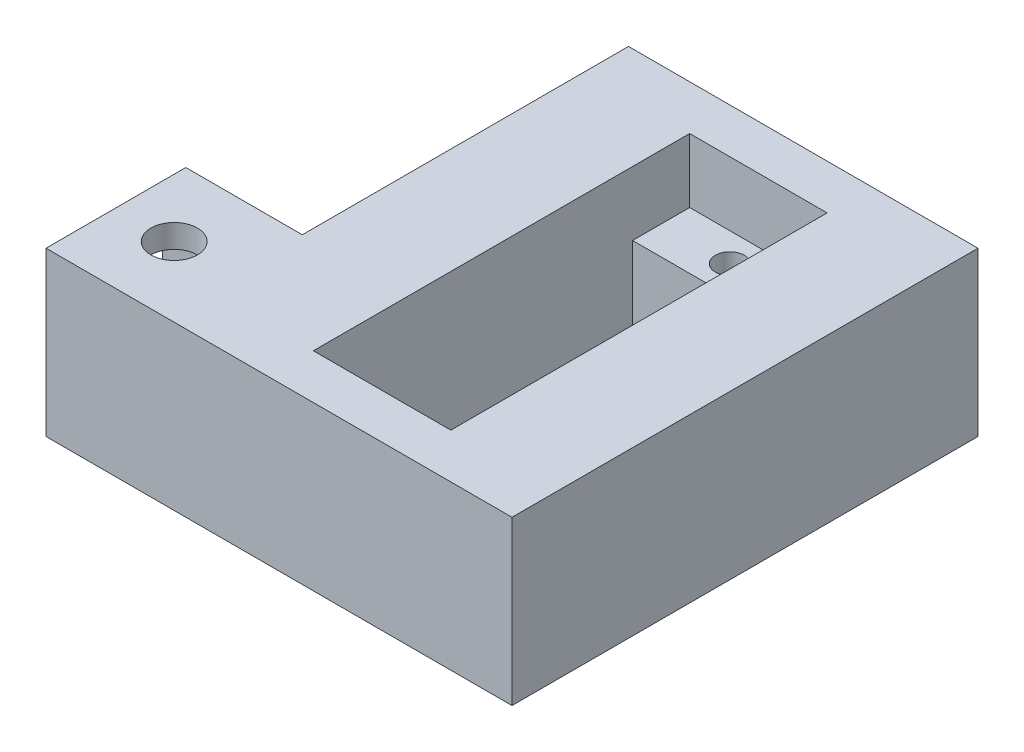
SolidWorks part; units mm, degrees
ref_plane "Front Plane" through (0, 0, 0) normal (0, 0, 1) x (1, 0, 0)
ref_plane "Top Plane" through (0, 0, 0) normal (0, 1, 0) x (1, 0, 0)
ref_plane "Right Plane" through (0, 0, 0) normal (1, 0, 0) x (0, 0, -1)
sketch "Sketch1" plane through (0, 0, 0) normal (0, 0, 1) x (1, 0, 0)
  line L1 (8.671, 9.0036) -> (-11.329, 9.0036)
  line L3 (11.4585, -4.9953) -> (8.671, -4.9953)
  line L5 (-11.329, -4.9953) -> (8.671, -4.9953)
  line L9 (8.671, 9.0036) -> (8.671, -4.9953)
  line L15 (-11.329, 9.0036) -> (-21.329, 9.0036)
  line L17 (-21.329, 9.0036) -> (-21.329, -4.9953)
  line L18 (-21.329, -4.9953) -> (-11.329, -4.9953)
  line L25 (18.8739, 13.2298) -> (8.671, 9.0036)
  line L26 (20.7873, 8.6104) -> (18.8739, 13.2298)
  line L27 (24.2314, 0.2955) -> (11.4585, -4.9953)
  line L28 (20.7873, 8.6104) -> (24.2314, 0.2955)
  dimension "D1" = 20
extrude "Boss-Extrude1" add sketch "Sketch1" along normal blind 40 contours L1 L15 L17 L18 L5 L9
sketch "Sketch3" plane through (0, 9.0036, 0) normal (0, 1, 0) x (1, 0, 0)
  line L0 (-6.329, -40) -> (-6.329, 0) construction
  line L1 (8.671, -40) -> (-21.329, -40) construction
  line L2 (-11.329, 0) -> (8.671, 0) construction
  line L3 (-21.329, -20) -> (8.671, -20) construction
  line L4 (-21.329, -40) -> (-21.329, 0) construction
  line L5 (8.671, -40) -> (8.671, 0) construction
  line L6 (-12.229, -31.25) -> (-0.429, -31.25)
  line L8 (-12.229, -3.85) -> (-12.229, -36.15)
  line L9 (-12.229, -36.15) -> (-0.429, -36.15)
  line L10 (-0.429, -3.85) -> (-0.429, -36.15)
  line L11 (-6.329, -31.25) -> (-6.329, -36.15) construction
  line L12 (-12.229, -3.85) -> (-0.429, -3.85)
  line L13 (-12.229, -8.75) -> (-0.429, -8.75)
  circle A0 centre (-6.329, -33.7) radius 1.25
  circle A1 centre (-6.329, -6.3) radius 1.25
  point P24 (-0.429, -20)
  point P26 (-12.229, -20)
  dimension "D1" = 11.8
  dimension "D2" = 5.9
  dimension "D3" = 16.15
  dimension "D4" = 4.9
sketch "Sketch4" plane through (0, 9.0036, 0) normal (0, 1, 0) x (1, 0, 0)
  line L0 (-12.229, -36.15) -> (-0.429, -36.15) construction
  line L1 (-0.429, -3.85) -> (-0.429, -36.15) construction
  line L2 (-12.229, -3.85) -> (-0.429, -3.85) construction
  line L3 (-12.229, -3.85) -> (-12.229, -36.15) construction
  line L4 (-12.229, -36.15) -> (-0.429, -36.15)
  line L5 (-0.429, -3.85) -> (-0.429, -36.15)
  line L6 (-12.229, -3.85) -> (-0.429, -3.85)
  line L7 (-12.229, -3.85) -> (-12.229, -36.15)
extrude "Cut-Extrude1" cut sketch "Sketch4" against normal blind 5.5
sketch "Sketch5" plane through (0, 3.5036, 0) normal (0, 1, 0) x (1, 0, 0)
  line L0 (-12.229, -31.25) -> (-0.429, -31.25) construction
  line L1 (-0.429, -3.85) -> (-0.429, -36.15) construction
  line L2 (-12.229, -3.85) -> (-12.229, -36.15) construction
  line L3 (-12.229, -8.75) -> (-0.429, -8.75) construction
  line L4 (-12.229, -31.25) -> (-0.429, -31.25)
  line L5 (-0.429, -8.75) -> (-0.429, -31.25)
  line L6 (-12.229, -8.75) -> (-12.229, -31.25)
  line L7 (-12.229, -8.75) -> (-0.429, -8.75)
extrude "Cut-Extrude2" cut sketch "Sketch5" against normal through all
sketch "Sketch6" plane through (0, 3.5036, 0) normal (0, 1, 0) x (1, 0, 0)
  circle A0 centre (-6.329, -6.3) radius 1.25
  circle A1 centre (-6.329, -33.7) radius 1.25
extrude "Cut-Extrude3" cut sketch "Sketch6" against normal through all
sketch "Sketch7" plane through (-21.329, 0, 0) normal (-1, 0, 0) x (0, 0, 1)
  line L0 (40, -4.9953) -> (0, -4.9953) construction
  line L5 (20, 9.0036) -> (20, -4.9953) construction
  line L6 (40, 9.0036) -> (0, 9.0036) construction
  line L7 (28, 9.0036) -> (28, -4.9953)
  line L8 (40, -4.9953) -> (28, -4.9953)
  line L9 (40, 9.0036) -> (40, -4.9953)
  line L10 (40, 9.0036) -> (28, 9.0036)
extrude "Boss-Extrude3" add sketch "Sketch7" along normal blind 10
sketch "Sketch11" plane through (-31.329, 0, 0) normal (-1, 0, 0) x (0, 0, 1)
  line L0 (40, 9.0036) -> (28, 9.0036) construction
  line L1 (30, 7.0036) -> (38, 7.0036)
  line L2 (30, 7.0036) -> (30, -2.9953)
  line L3 (30, -2.9953) -> (38, -2.9953)
  line L4 (38, 7.0036) -> (38, -2.9953)
  line L5 (28, -4.9953) -> (40, -4.9953) construction
  line L6 (40, -4.9953) -> (40, 9.0036) construction
  line L7 (28, 9.0036) -> (28, -4.9953) construction
  dimension "D1" = 2
  dimension "D2" = 2
  dimension "D3" = 2
  dimension "D4" = 2
extrude "Cut-Extrude5" cut sketch "Sketch11" against normal blind 10
sketch "Sketch12" plane through (0, 9.0036, 0) normal (0, 1, 0) x (1, 0, 0)
  line L5 (-26.329, -28) -> (-26.329, -40) construction
  line L6 (-31.329, -34) -> (-21.329, -34) construction
  circle A0 centre (-26.329, -34) radius 2
extrude "Cut-Extrude6" cut sketch "Sketch12" against normal through all
